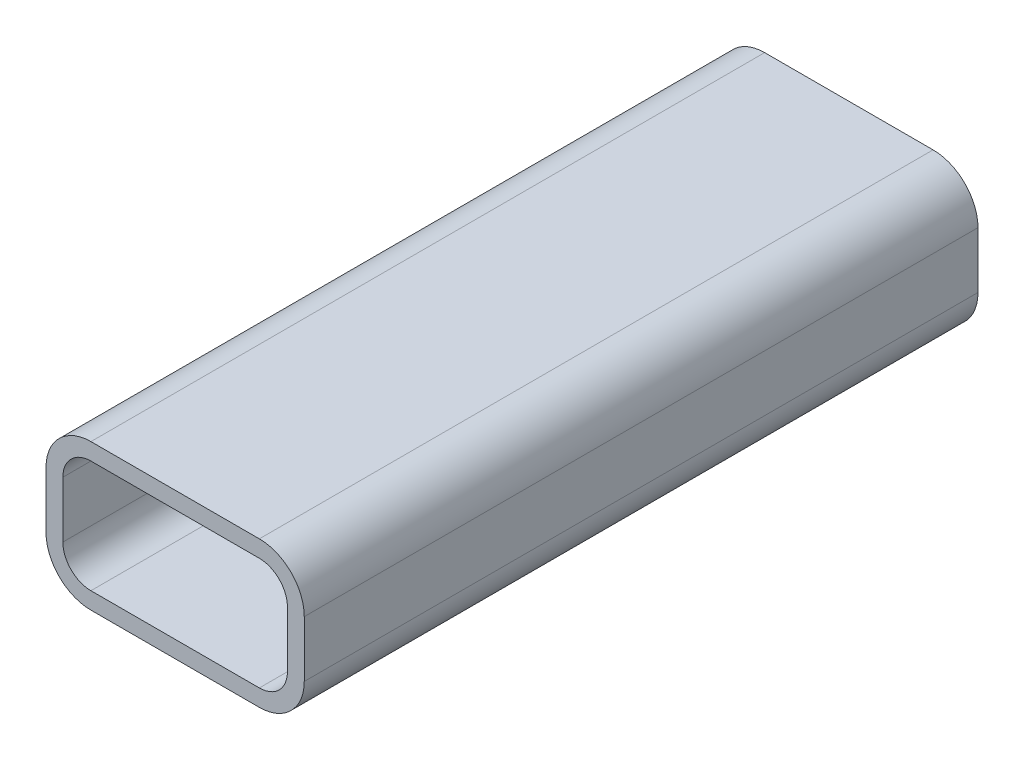
SolidWorks part; units mm, degrees
ref_plane "Front Plane" through (0, 0, 0) normal (0, 0, 1) x (1, 0, 0)
ref_plane "Top Plane" through (0, 0, 0) normal (0, 1, 0) x (1, 0, 0)
ref_plane "Right Plane" through (0, 0, 0) normal (1, 0, 0) x (0, 0, -1)
sketch "Sketch1" plane through (0, 0, 0) normal (0, 0, 1) x (1, 0, 0)
  line L1 (-5.9483, 0.9483) -> (24.0517, 0.9483)
  line L2 (-10.9483, -4.0517) -> (-10.9483, -14.0517)
  line L3 (-5.9483, -19.0517) -> (24.0517, -19.0517)
  line L4 (29.0517, -4.0517) -> (29.0517, -14.0517)
  arc A0 (24.0517, -19.0517) -> (29.0517, -14.0517) centre (24.0517, -14.0517) ccw
  arc A1 (-10.9483, -14.0517) -> (-5.9483, -19.0517) centre (-5.9483, -14.0517) ccw
  arc A2 (-5.9483, 0.9483) -> (-10.9483, -4.0517) centre (-5.9483, -4.0517) ccw
  arc A3 (24.0517, 0.9483) -> (29.0517, -4.0517) centre (24.0517, -4.0517) cw
  point P0 (0, 0)
  dimension "D2" = 5
  dimension "Length" = 40
  dimension "Height" = 20
extrude "Extrude-Thin1" add sketch "Sketch1" along normal mid plane 120 thin thin type one direction wall 3
sketch "Sketch3" plane through (0, 3.9483, 0) normal (0, 1, 0) x (1, 0, 0)
  line L0 (0, 45) -> (0, -45) construction
  line L1 (6, 45) -> (6, -45)
  line L2 (-6, 45) -> (-6, -45)
  arc A0 (6, 45) -> (-6, 45) centre (0, 45) ccw
  arc A1 (-6, -45) -> (6, -45) centre (0, -45) ccw
  point P3 (0, 0)
  dimension "D2" = 6
  dimension "D1" = 90
extrude "Cut-Extrude1" [suppressed] cut sketch "Sketch3" against normal through all
